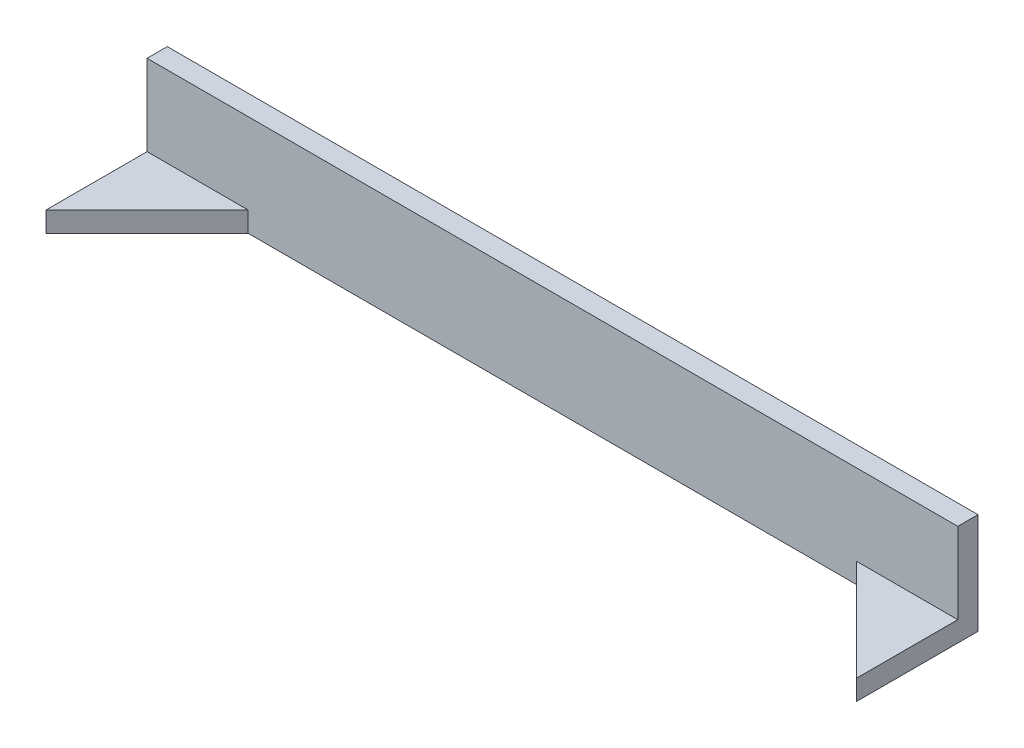
SolidWorks part; units mm, degrees
ref_plane "Front Plane" through (0, 0, 0) normal (0, 0, 1) x (1, 0, 0)
ref_plane "Top Plane" through (0, 0, 0) normal (0, 1, 0) x (1, 0, 0)
ref_plane "Right Plane" through (0, 0, 0) normal (1, 0, 0) x (0, 0, -1)
sketch "Sketch1" plane through (0, 0, 0) normal (1, 0, 0) x (0, 0, -1)
  line L1 (-19, 95) -> (19, 95)
  line L2 (-19, 95) -> (-19, -95)
  line L3 (-19, -95) -> (19, -95)
  line L4 (19, 95) -> (19, -95)
  line L5 (-19, 95) -> (19, -95) construction
  line L6 (-19, -95) -> (19, 95) construction
  point P0 (0, 0)
  dimension "D1" = 190
  dimension "D2" = 38
extrude "Boss-Extrude1" add sketch "Sketch1" along normal blind 1524
sketch "Sketch2" plane through (0, 0, 19) normal (0, 0, 1) x (1, 0, 0)
  line L0 (762, 95) -> (762, -95) construction
  line L1 (0, -95) -> (190, -95)
  line L2 (0, -95) -> (0, -57)
  line L3 (0, -57) -> (190, -57)
  line L4 (190, -95) -> (190, -57)
  line L5 (1524, 95) -> (0, 95) construction
  line L6 (1524, -95) -> (0, -95) construction
  line L7 (1524, -57) -> (1334, -57)
  line L8 (1334, -95) -> (1334, -57)
  line L9 (1524, -95) -> (1334, -95)
  line L10 (1524, -95) -> (1524, -57)
  dimension "D1" = 38
  dimension "D2" = 190
extrude "Boss-Extrude2" add sketch "Sketch2" along normal blind 190
sketch "Sketch3" plane through (0, -57, 0) normal (0, 1, 0) x (1, 0, 0)
  line L0 (190, -19) -> (0, -209)
  line L1 (0, -209) -> (190, -209)
  line L2 (190, -209) -> (190, -19)
  line L3 (1334, -19) -> (1524, -209)
  line L4 (1524, -209) -> (1334, -209)
  line L5 (1334, -209) -> (1334, -19)
extrude "Cut-Extrude1" cut sketch "Sketch3" against normal blind 190
